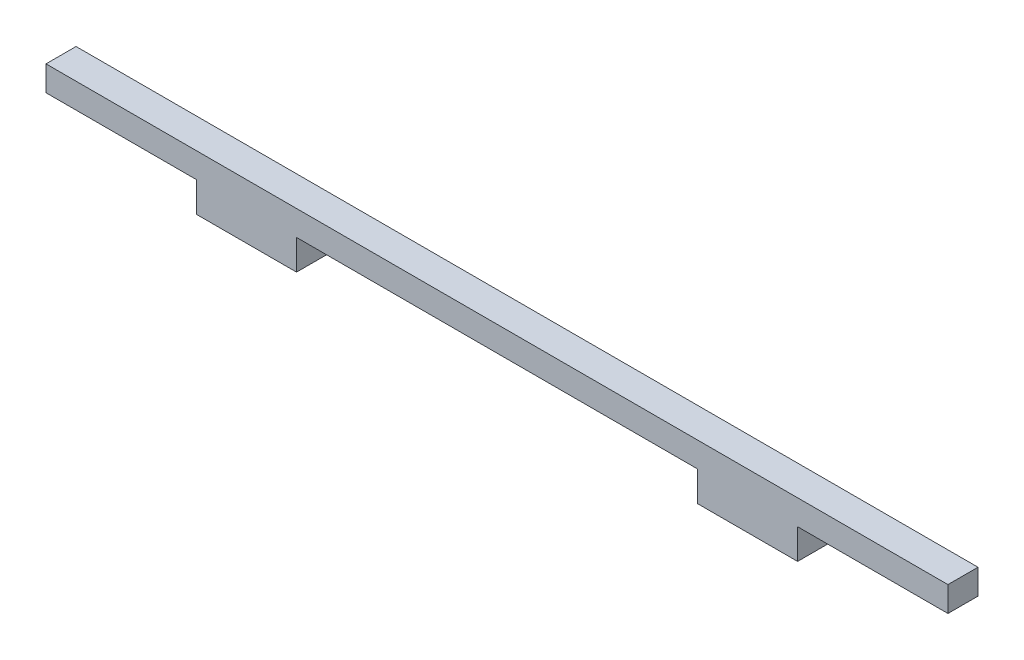
SolidWorks part; units mm, degrees
ref_plane "Front Plane" through (0, 0, 0) normal (0, 0, 1) x (1, 0, 0)
ref_plane "Top Plane" through (0, 0, 0) normal (0, 1, 0) x (1, 0, 0)
ref_plane "Right Plane" through (0, 0, 0) normal (1, 0, 0) x (0, 0, -1)
sketch "Sketch1" plane through (0, 0, 0) normal (0, 0, 1) x (1, 0, 0)
  line L0 (-45, 0) -> (45, 0)
  line L1 (45, 0) -> (45, -2.5)
  line L2 (45, -2.5) -> (30, -2.5)
  line L3 (30, -2.5) -> (30, -5.5)
  line L4 (30, -5.5) -> (20, -5.5)
  line L5 (20, -5.5) -> (20, -2.5)
  line L6 (20, -2.5) -> (-20, -2.5)
  line L7 (-20, -2.5) -> (-20, -5.5)
  line L8 (-20, -5.5) -> (-30, -5.5)
  line L9 (-30, -5.5) -> (-30, -2.5)
  line L10 (-30, -2.5) -> (-45, -2.5)
  line L11 (-45, -2.5) -> (-45, 0)
  dimension "D1" = 90
  dimension "D2" = 2.5
  dimension "D3" = 3
  dimension "D4" = 2.5
  dimension "D5" = 3
  dimension "D6" = 10
  dimension "D7" = 15
  dimension "D8" = 15
  dimension "D9" = 10
  dimension "D10" = 3
  dimension "D11" = 45
extrude "Boss-Extrude1" add sketch "Sketch1" along normal blind 3
